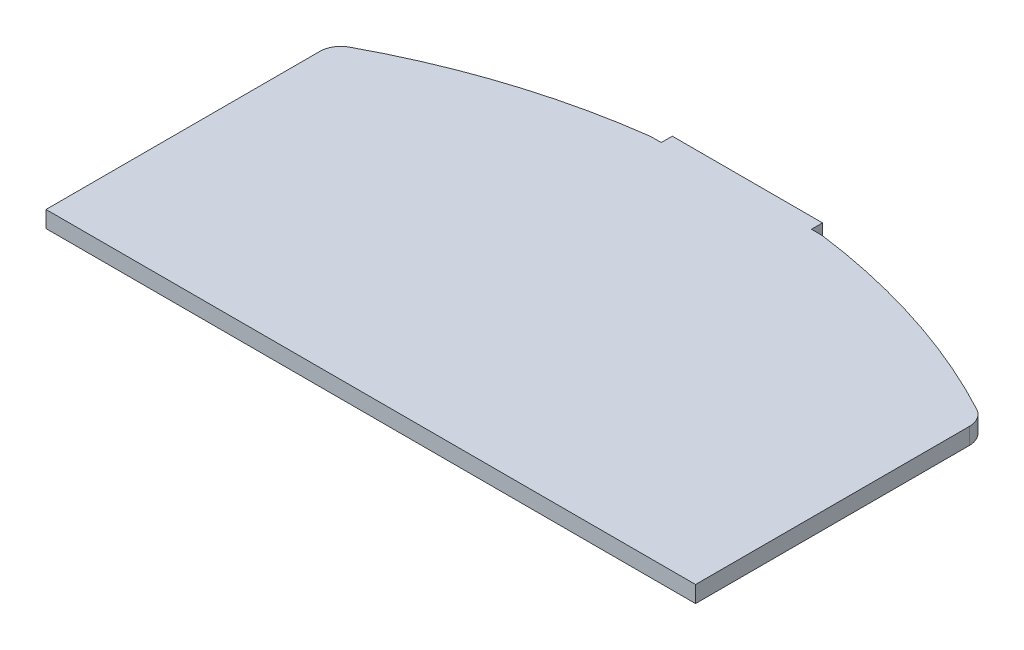
SolidWorks part; units mm, degrees
ref_plane "Спереди" through (0, 0, 0) normal (0, 0, 1) x (1, 0, 0)
ref_plane "Сверху" through (0, 0, 0) normal (0, 1, 0) x (1, 0, 0)
ref_plane "Справа" through (0, 0, 0) normal (1, 0, 0) x (0, 0, -1)
other "Configuration Table"
sketch "Sketch1" plane through (0, 0, 0) normal (0, 1, 0) x (1, 0, 0)
  line L13 (29.4, -10.9094) -> (29.4, -35.694)
  line L14 (7.6112, -2.6) -> (6.8, -2.6)
  line L19 (6.8, -1.6) -> (6.8, -2.6)
  line L25 (29.4, -35.694) -> (-29.4, -35.694)
  line L27 (-6.8, -1.6) -> (-6.8, -2.6)
  line L28 (-7.6112, -2.6) -> (-6.8, -2.6)
  line L29 (-29.4, -10.9094) -> (-29.4, -35.694)
  line L30 (-6.8, -1.6) -> (6.8, -1.6)
  arc A12 (28.398, -9.2351) -> (29.4, -10.9094) centre (27.5, -10.9094) cw
  arc A13 (7.6112, -2.6) -> (7.8598, -2.6163) centre (7.6112, -4.5) cw
  arc A14 (7.8598, -2.6163) -> (28.398, -9.2351) centre (0, -62.1804) cw
  arc A18 (-7.6112, -2.6) -> (-7.8598, -2.6163) centre (-7.6112, -4.5) ccw
  arc A19 (-7.8598, -2.6163) -> (-28.398, -9.2351) centre (0, -62.1804) ccw
  arc A20 (-28.398, -9.2351) -> (-29.4, -10.9094) centre (-27.5, -10.9094) ccw
  point P2 (0, 0)
  point P22 (0, -1.1)
extrude "Boss-Extrude1" add sketch "Sketch1" along normal blind 1.5
